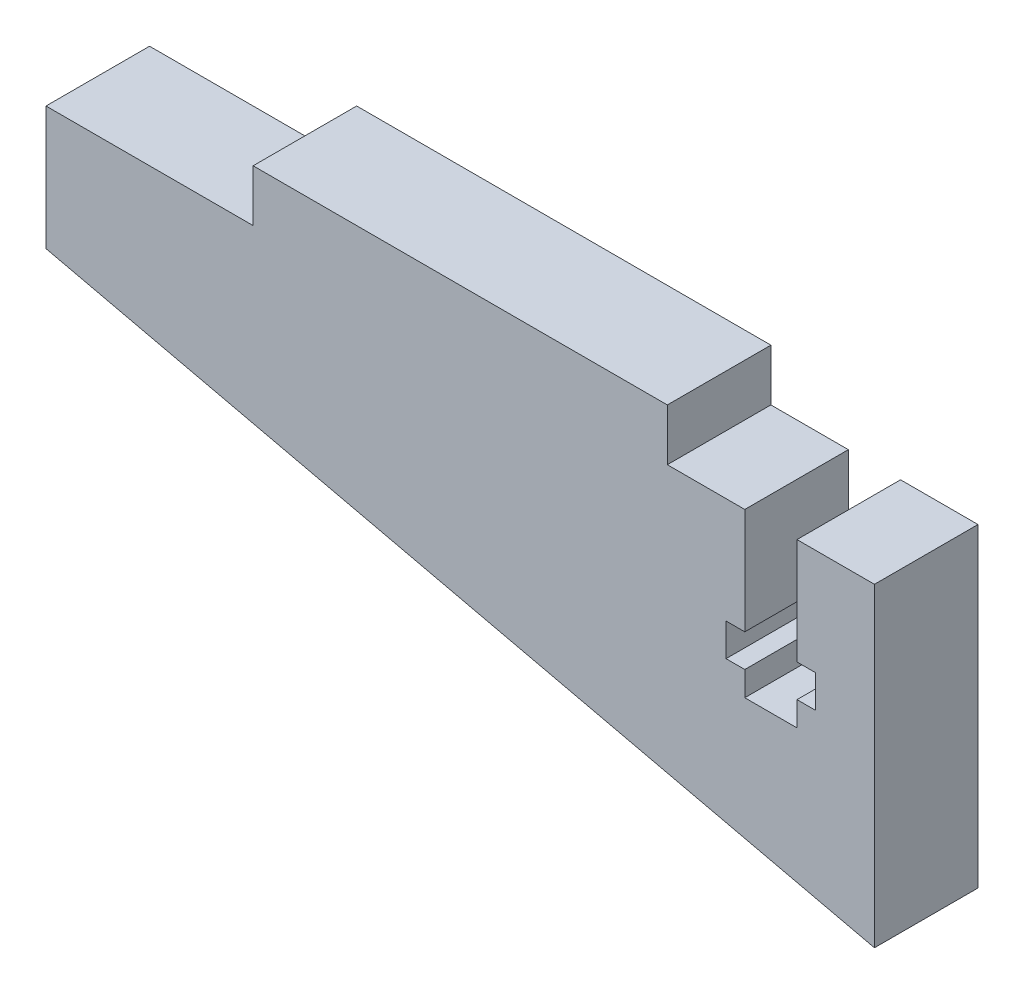
SolidWorks part; units mm, degrees
ref_plane "Front Plane" through (0, 0, 0) normal (0, 0, 1) x (1, 0, 0)
ref_plane "Top Plane" through (0, 0, 0) normal (0, 1, 0) x (1, 0, 0)
ref_plane "Right Plane" through (0, 0, 0) normal (1, 0, 0) x (0, 0, -1)
sketch "Sketch1" plane through (0, 0, 0) normal (0, 0, 1) x (1, 0, 0)
  line L0 (53.037, -0.1666) -> (2.237, 11.5615)
  line L1 (14.937, 20.7249) -> (2.237, 20.7249) construction
  line L2 (2.237, 11.5615) -> (2.237, 19.1374)
  line L3 (2.237, 19.1374) -> (14.937, 19.1374)
  line L4 (53.037, -0.1666) -> (53.037, 19.1374)
  line L5 (46.687, 9.1374) -> (53.037, 9.1374) construction
  line L6 (14.937, 19.1374) -> (14.937, 22.3124)
  line L7 (14.937, 22.3124) -> (40.337, 22.3124)
  line L8 (40.337, 19.1374) -> (40.337, 22.3124)
  line L9 (2.237, 20.7249) -> (2.237, 19.1374) construction
  line L10 (40.337, 19.1374) -> (45.087, 19.1374)
  line L12 (45.087, 19.1374) -> (45.087, 12.6374)
  line L13 (45.087, 9.1374) -> (48.287, 9.1374)
  line L14 (48.287, 19.1374) -> (48.287, 12.6374)
  line L15 (40.337, 9.1374) -> (46.687, 9.1374) construction
  line L16 (43.937, 11.6374) -> (49.437, 11.6374) construction
  line L17 (45.087, 12.6374) -> (43.937, 12.6374)
  line L18 (48.287, 10.6374) -> (48.287, 9.1374)
  line L19 (45.087, 10.6374) -> (43.937, 10.6374)
  line L20 (43.937, 12.6374) -> (43.937, 10.6374)
  line L21 (48.287, 12.6374) -> (49.437, 12.6374)
  line L22 (48.287, 19.1374) -> (53.037, 19.1374)
  line L23 (48.287, 10.6374) -> (49.437, 10.6374)
  line L24 (49.437, 12.6374) -> (49.437, 10.6374)
  line L25 (45.087, 10.6374) -> (45.087, 9.1374)
  dimension "D1" = 77
  dimension "D2" = 19.304
  dimension "D3" = 3.175
  dimension "D4" = 25.4
  dimension "D5" = 50.8
  dimension "D6" = 12.7
  dimension "D7" = 3.2
  dimension "D8" = 5.5
  dimension "D9" = 2
  dimension "D10" = 7.5
  dimension "D11" = 10
extrude "Boss-Extrude1" add sketch "Sketch1" along normal blind 6.35 contours L7 L8 L10 L12 L17 L20 L19 L25 L13 L18 L23 L24 L21 L14 L22 L4 L0 L2 L3 L6
